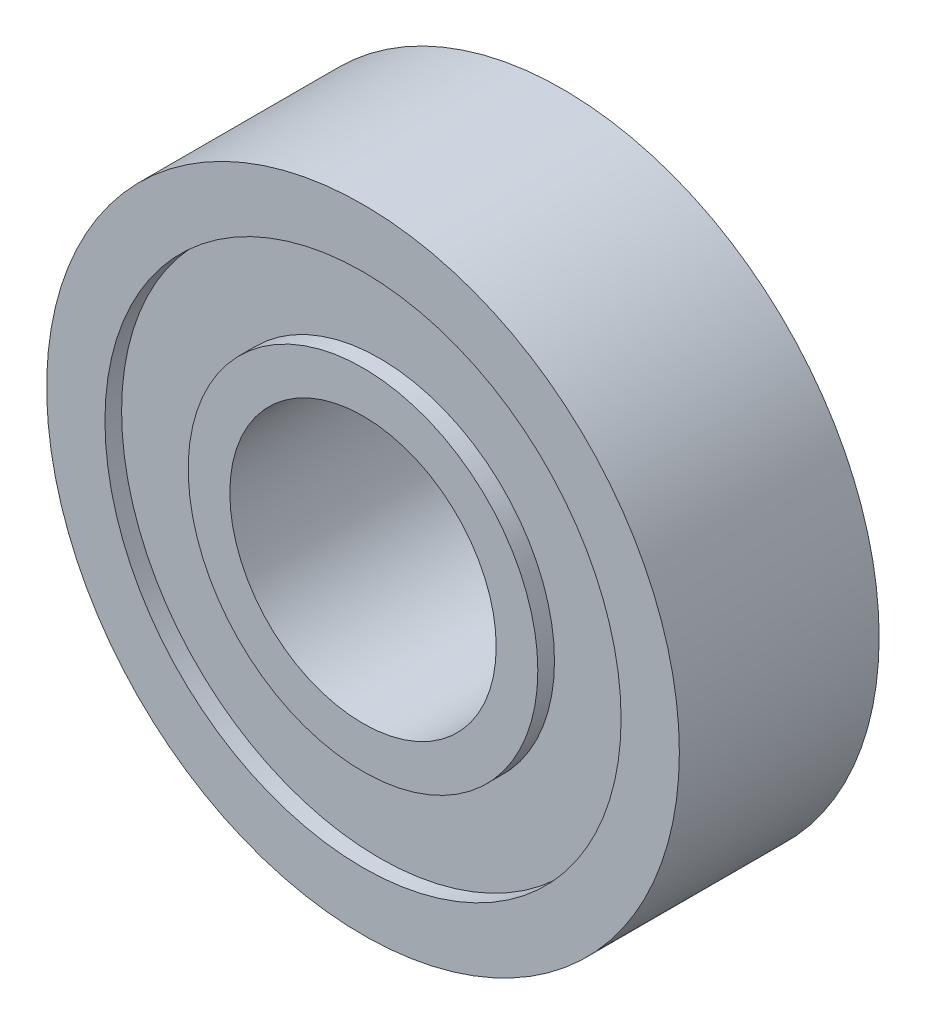
SolidWorks part; units mm, degrees
material "201 退火不鏽鋼 (SS)"
ref_plane "前基準面" through (0, 0, 0) normal (0, 0, 1) x (1, 0, 0)
ref_plane "上基準面" through (0, 0, 0) normal (0, 1, 0) x (1, 0, 0)
ref_plane "右基準面" through (0, 0, 0) normal (1, 0, 0) x (0, 0, -1)
sketch "草圖1" plane through (0, 0, 0) normal (0, 0, 1) x (1, 0, 0)
  circle A0 centre (0, 0) radius 9.5
  dimension "D1" = 19
extrude "填料-伸長1" add sketch "草圖1" along normal mid plane 6
sketch "草圖2" plane through (0, 0, 3) normal (0, 0, 1) x (1, 0, 0)
  circle A0 centre (0, 0) radius 4
  dimension "D1" = 8
extrude "除料-伸長1" cut sketch "草圖2" against normal through all
sketch "草圖3" plane through (0, 0, 3) normal (0, 0, 1) x (1, 0, 0)
  circle A0 centre (0, 0) radius 5.25
  circle A1 centre (0, 0) radius 7.75
  dimension "D1" = 15.5
  dimension "D2" = 10.5
extrude "除料-伸長2" cut sketch "草圖3" against normal blind 0.5
mirror "鏡射1" about plane through (0, 0, 0) normal (0, 0, 1) of "除料-伸長2"
